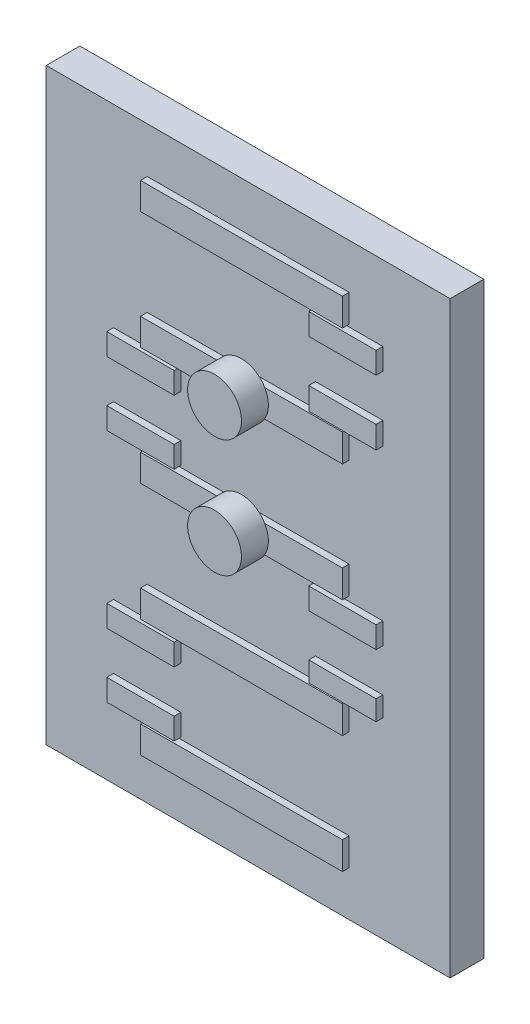
SolidWorks part; units mm, degrees
ref_plane "Front Plane" through (0, 0, 0) normal (0, 0, 1) x (1, 0, 0)
ref_plane "Top Plane" through (0, 0, 0) normal (0, 1, 0) x (1, 0, 0)
ref_plane "Right Plane" through (0, 0, 0) normal (1, 0, 0) x (0, 0, -1)
sketch "Sketch1" plane through (0, 0, 0) normal (0, 0, 1) x (1, 0, 0)
  line L1 (-9.525, 13.8748) -> (9.525, 13.8748)
  line L2 (-9.525, 13.8748) -> (-9.525, -13.8748)
  line L3 (-9.525, -13.8748) -> (9.525, -13.8748)
  line L4 (9.525, 13.8748) -> (9.525, -13.8748)
  dimension "D1" = 27.7495
  dimension "D2" = 13.8748
  dimension "D3" = 19.05
  dimension "D4" = 9.525
extrude "Boss-Extrude1" add sketch "Sketch1" along normal blind 1.5875
hole_wizard "#0-80 Tapped Hole1" positions "Sketch3" profile "Sketch2" tap size "#0-80" standard "ANSI Inch" end condition through all
sketch "Sketch3" plane through (0, 0, 1.5875) normal (0, 0, 1) x (1, 0, 0)
  line L0 (9.525, 13.8748) -> (-9.525, 13.8748) construction
  point P0 (0, -11.0998)
  point P2 (0, -5.5499)
  point P5 (0, 0)
  point P7 (0, 5.5499)
  point P9 (0, 11.0998)
  dimension "D1" = 5.5499
  dimension "D2" = 5.5499
  dimension "D3" = 5.5499
  dimension "D4" = 5.5499
  dimension "D5" = 2.775
sketch "Sketch2" plane through (0, -11.0998, 1.5875) normal (1, 0, 0) x (0, -1, 0)
  line L0 (0, 0) -> (0, 1.5875)
  line L1 (0, 1.5875) -> (0.5956, 1.5875)
  line L2 (0.5956, 1.5875) -> (0.5956, 0)
  line L5 (0.5956, 0) -> (0, 0)
  line L11 (0, -6.35) -> (0, 107.95) construction
  dimension "Thread Major Dia." = 1.1913
  dimension "Thru Tap Drill Depth" = 1.5875
sketch "Sketch4" plane through (0, 0, 1.5875) normal (0, 0, 1) x (1, 0, 0)
  line L0 (3.175, -4.8387) -> (6.35, -4.8387)
  line L1 (-6.35, -10.3886) -> (-3.175, -10.3886)
  line L2 (-6.35, -10.3886) -> (-6.35, -9.3726)
  line L3 (-6.35, -9.3726) -> (-3.175, -9.3726)
  line L4 (-3.175, -10.3886) -> (-3.175, -9.3726)
  line L5 (-6.35, -7.366) -> (-3.175, -7.366)
  line L6 (-6.35, -7.366) -> (-6.35, -6.35)
  line L7 (-6.35, -6.35) -> (-3.175, -6.35)
  line L8 (-3.175, -7.366) -> (-3.175, -6.35)
  line L9 (3.175, -4.8387) -> (3.175, -3.8989)
  line L10 (3.175, -3.8989) -> (6.35, -3.8989)
  line L11 (6.35, -4.8387) -> (6.35, -3.8989)
  line L12 (3.175, -1.8923) -> (6.35, -1.8923)
  line L13 (3.175, -1.8923) -> (3.175, -0.8763)
  line L14 (3.175, -0.8763) -> (6.35, -0.8763)
  line L15 (6.35, -1.8923) -> (6.35, -0.8763)
  line L16 (-6.35, 0.7112) -> (-3.175, 0.7112)
  line L17 (-6.35, 0.7112) -> (-6.35, 1.7272)
  line L18 (-6.35, 1.7272) -> (-3.175, 1.7272)
  line L19 (-3.175, 0.7112) -> (-3.175, 1.7272)
  line L20 (-6.35, 3.7338) -> (-3.175, 3.7338)
  line L21 (-6.35, 3.7338) -> (-6.35, 4.7498)
  line L22 (-6.35, 4.7498) -> (-3.175, 4.7498)
  line L23 (-3.175, 3.7338) -> (-3.175, 4.7498)
  line L24 (3.175, 6.2611) -> (6.35, 6.2611)
  line L25 (3.175, 6.2611) -> (3.175, 7.3111)
  line L26 (3.175, 7.3111) -> (6.35, 7.3111)
  line L27 (6.35, 6.2611) -> (6.35, 7.3111)
  line L28 (3.175, 9.3177) -> (6.35, 9.3177)
  line L29 (3.175, 9.3177) -> (3.175, 10.3337)
  line L30 (3.175, 10.3337) -> (6.35, 10.3337)
  line L31 (6.35, 9.3177) -> (6.35, 10.3337)
  dimension "D1" = 1.016
  dimension "D2" = 3.175
  dimension "D3" = 1.016
  dimension "D4" = 3.175
  dimension "D5" = 2.0066
  dimension "D6" = 0.7112
  dimension "D7" = 3.175
  dimension "D8" = 3.175
  dimension "D9" = 3.175
  dimension "D10" = 1.016
  dimension "D11" = 3.175
  dimension "D12" = 2.0066
  dimension "D13" = 0.7112
  dimension "D14" = 3.175
  dimension "D15" = 3.175
  dimension "D16" = 1.016
  dimension "D17" = 3.175
  dimension "D18" = 2.0066
  dimension "D19" = 3.175
  dimension "D20" = 1.016
  dimension "D21" = 3.175
  dimension "D22" = 2.0066
  dimension "D23" = 3.175
  dimension "D24" = 3.175
  dimension "D25" = 0.7112
  dimension "D26" = 0.7112
extrude "Boss-Extrude2" add sketch "Sketch4" along normal blind 0.3175
sketch "Sketch6" plane through (0, 0, 1.5875) normal (0, 0, 1) x (1, 0, 0)
  line L1 (4.7625, -10.4479) -> (-4.7625, -10.4817)
  line L2 (4.7625, -10.4479) -> (4.7625, -11.7517)
  line L3 (4.7625, -11.7517) -> (-4.7625, -11.7517)
  line L4 (-4.7625, -10.4817) -> (-4.7625, -11.7517)
  dimension "D1" = 9.525
  dimension "D2" = 4.7625
  dimension "D3" = 1.27
  dimension "D4" = 0.635
extrude "Boss-Extrude3" add sketch "Sketch6" along normal blind 0.3175
pattern_linear "LPattern1" count 5 spacing 5.5499 along (0, 1, 0) of "Boss-Extrude3"
sketch "Sketch8" plane through (0, 0, 1.905) normal (0, 0, 1) x (1, 0, 0)
  circle A0 centre (0, 0) radius 1.27
  circle A1 centre (0, 5.5499) radius 1.27
  dimension "D1" = 2.54
  dimension "D2" = 2.54
extrude "Boss-Extrude4" add sketch "Sketch8" along normal blind 1.27
equation "\"D2@Sketch1\"=\"D1@Sketch1\"/2"
equation "\"D4@Sketch1\"=\"D3@Sketch1\"/2"
equation "\"D3@Sketch3\"=\"D2@Sketch3\""
equation "\"D4@Sketch3\"=\"D1@Sketch3\""
equation "\"D2@Sketch3\"=\"D1@Sketch3\""
equation "\"D8@Sketch4\"=\"D7@Sketch4\""
equation "\"D13@Sketch4\"=\"D6@Sketch4\""
equation "\"D14@Sketch4\"=\"D7@Sketch4\""
equation "\"D23@Sketch4\"=\"D8@Sketch4\""
equation "\"D24@Sketch4\"=\"D8@Sketch4\""
equation "\"D25@Sketch4\"=\"D6@Sketch4\""
equation "\"D26@Sketch4\"=\"D6@Sketch4\""
equation "\"D2@Sketch6\"=\"D1@Sketch6\"/2"
equation "\"D4@Sketch6\"=\"D3@Sketch6\"/2"
equation "\"D2@Sketch8\"=\"D1@Sketch8\""
